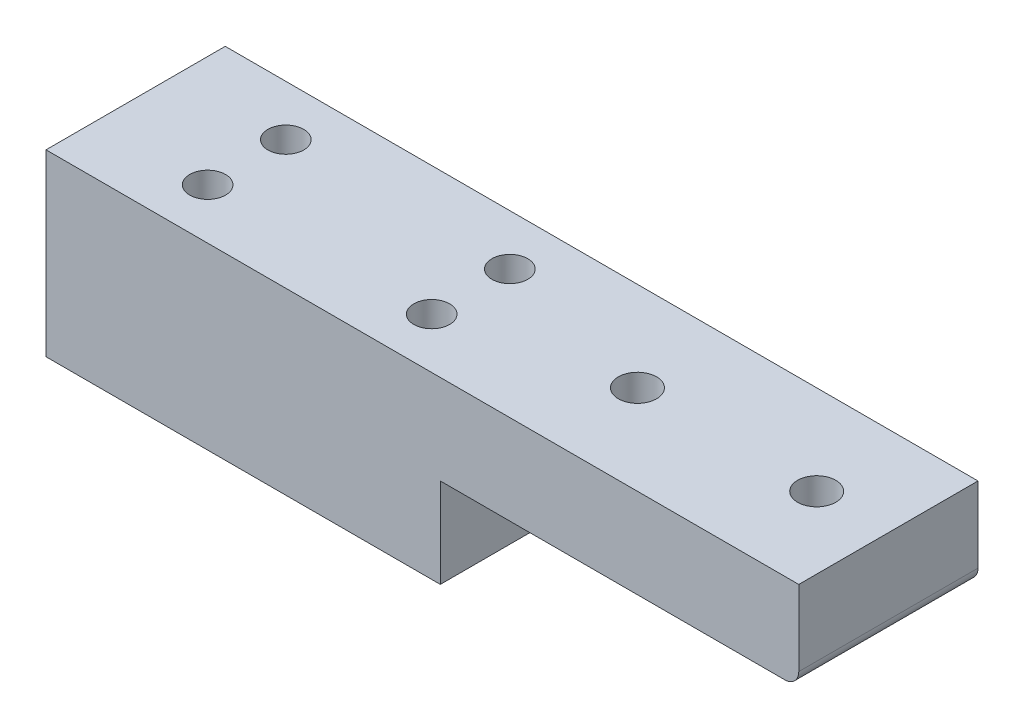
SolidWorks part; units mm, degrees
ref_plane "Front Plane" through (0, 0, 0) normal (0, 0, 1) x (1, 0, 0)
ref_plane "Top Plane" through (0, 0, 0) normal (0, 1, 0) x (1, 0, 0)
ref_plane "Right Plane" through (0, 0, 0) normal (1, 0, 0) x (0, 0, -1)
sketch "Sketch2" plane through (0, 0, 0) normal (0, 1, 0) x (1, 0, 0)
  line L1 (0, 0) -> (25.4, 0)
  line L2 (0, 0) -> (0, -12.7)
  line L3 (0, -12.7) -> (25.4, -12.7)
  line L4 (25.4, 0) -> (25.4, -12.7)
  dimension "D1" = 12.7
  dimension "D2" = 25.4
extrude "Boss-Extrude1" add sketch "Sketch2" along normal blind 6.35
sketch "Sketch3" plane through (0, 0, 0) normal (0, -1, 0) x (1, 0, 0)
  line L0 (0, 12.7) -> (25.4, 12.7) construction
  line L2 (0, 0) -> (0, 12.7) construction
  circle A0 centre (5.334, 9.1186) radius 0.5461
  circle A1 centre (5.334, 3.5814) radius 0.5461
  circle A2 centre (21.209, 3.5814) radius 0.5461
  circle A3 centre (21.209, 9.1186) radius 0.5461
  dimension "D1" = 1.0922
  dimension "D2" = 1.0922
  dimension "D3" = 1.0922
  dimension "D4" = 1.0922
  dimension "D5" = 5.5372
  dimension "D6" = 5.5372
  dimension "D8" = 5.334
  dimension "D7" = 3.5814
  dimension "D9" = 15.875
extrude "Cut-Extrude1" cut sketch "Sketch3" against normal through all
sketch "Sketch4" plane through (0, 6.35, 0) normal (0, 1, 0) x (1, 0, 0)
  line L0 (25.4, -12.7) -> (25.4, 0) construction
  line L1 (0, -12.7) -> (50.8, -12.7)
  line L2 (0, -12.7) -> (0, 0)
  line L3 (0, 0) -> (50.8, 0)
  line L4 (50.8, -12.7) -> (50.8, 0)
  dimension "D1" = 25.4
  dimension "D2" = 12.7
extrude "Boss-Extrude2" add sketch "Sketch4" along normal blind 6.35
sketch "Sketch5" plane through (0, 12.7, 0) normal (0, 1, 0) x (1, 0, 0)
  line L1 (50.8, -12.7) -> (50.8, 0) construction
  circle A0 centre (45.72, -6.35) radius 1.9
  circle A1 centre (33.02, -6.35) radius 1.905
  point P9 (50.8, -6.35)
  dimension "D3" = 3.8
  dimension "D4" = 3.81
  dimension "D1" = 12.7
  dimension "D2" = 5.08
sketch "Sketch6" plane through (0, 0, 0) normal (0, -1, 0) x (1, 0, 0)
  circle A0 centre (5.334, 9.1186) radius 0.5461
  circle A1 centre (5.334, 3.5814) radius 0.5461
  circle A2 centre (21.209, 3.5814) radius 0.5461
  circle A3 centre (21.209, 9.1186) radius 0.5461
  dimension "D1" = 1.0922
sketch "Sketch7" plane through (0, 0, 0) normal (-1, 0, 0) x (0, 0, 1)
  line L0 (0, 12.7) -> (12.7, 12.7) construction
  line L1 (0, 12.7) -> (0, 0) construction
  circle A1 centre (6.35, 6.35) radius 0.9914
  point P0 (6.35, 6.35)
  point P4 (6.35, 12.7)
  point P11 (0, 6.35)
hole_wizard "#8 (0.199) Diameter Hole1" positions "Sketch13" profile "Sketch14" hole size "#8" standard "ANSI Inch" end condition through all
sketch "Sketch13" plane through (0, 0, 0) normal (0, -1, 0) x (-1, 0, 0)
  point P0 (-5.334, -3.5814)
  point P3 (-21.209, -3.5814)
  point P6 (-21.209, -9.1186)
  point P9 (-5.334, -9.1186)
sketch "Sketch14" plane through (5.334, 0, 3.5814) normal (1, 0, 0) x (0, 0, -1)
  line L0 (0, 0) -> (0, 12.7)
  line L1 (0, 12.7) -> (1.27, 12.7)
  line L2 (1.27, 12.7) -> (1.27, 0)
  line L5 (1.27, 0) -> (0, 0)
  line L11 (0, -6.35) -> (0, 107.95) construction
  dimension "Thru Hole Dia." = 2.54
  dimension "Thru Hole Depth" = 12.7
hole_wizard "#6-32 Tapped Hole3" positions "Sketch15" profile "Sketch16" tap size "#6-32" standard "ANSI Inch" end condition through all
sketch "Sketch15" plane through (0, 6.35, 0) normal (0, -1, 0) x (-1, 0, 0)
  point P0 (-33.02, -6.35)
  point P4 (-45.72, -6.35)
sketch "Sketch16" plane through (33.02, 6.35, 6.35) normal (1, 0, 0) x (0, 0, -1)
  line L0 (0, 0) -> (0, 6.35)
  line L1 (0, 6.35) -> (1.3525, 6.35)
  line L2 (1.3525, 6.35) -> (1.3525, 0)
  line L5 (1.3525, 0) -> (0, 0)
  line L11 (0, -6.35) -> (0, 107.95) construction
  dimension "Thru Tap Drill Dia." = 2.7051
  dimension "Thru Tap Drill Depth" = 6.35
cosmetic thread "Hole Thread1" parameters "D2"=3.5052
cosmetic thread "Hole Thread2" parameters "D2"=3.5052
fillet "Fillet1" radius 1 1 edges at (50.8, 6.35, 6.35)
sketch "Sketch17" plane through (0, 0, 0) normal (-1, 0, 0) x (0, 0, 1)
  line L1 (12.7, 12.7) -> (0, 12.7)
  line L2 (12.7, 12.7) -> (12.7, 0)
  line L3 (12.7, 0) -> (0, 0)
  line L4 (0, 12.7) -> (0, 0)
extrude "Boss-Extrude3" add sketch "Sketch17" along normal blind 2.54
sketch "Sketch18" plane through (-2.54, 0, 0) normal (-1, 0, 0) x (0, 0, 1)
  point P0 (6.35, 6.35)
hole_wizard "#6-32 Tapped Hole4" positions "Sketch19" profile "Sketch20" tap size "#6-32" standard "ANSI Inch"
sketch "Sketch19" plane through (-2.54, 0, 0) normal (-1, 0, 0) x (0, 0, 1)
  point P0 (6.35, 6.35)
sketch "Sketch20" plane through (-2.54, 6.35, 6.35) normal (0, 1, 0) x (0, 0, 1)
  line L0 (0, 0) -> (0, 6.2991)
  line L1 (0, 6.2991) -> (1.3525, 5.4864)
  line L2 (1.3525, 5.4864) -> (1.3525, 0)
  line L5 (1.3525, 0) -> (0, 0)
  line L10 (0, 6.2991) -> (-1.3526, 5.4864) construction
  line L11 (0, -6.35) -> (0, 107.95) construction
  dimension "Tap Drill Dia." = 2.7051
  dimension "Tap Drill Depth" = 5.4864
  dimension "Drill Angle" = 118
cosmetic thread "Hole Thread3" parameters "D1"=5.08, "D2"=3.5052
